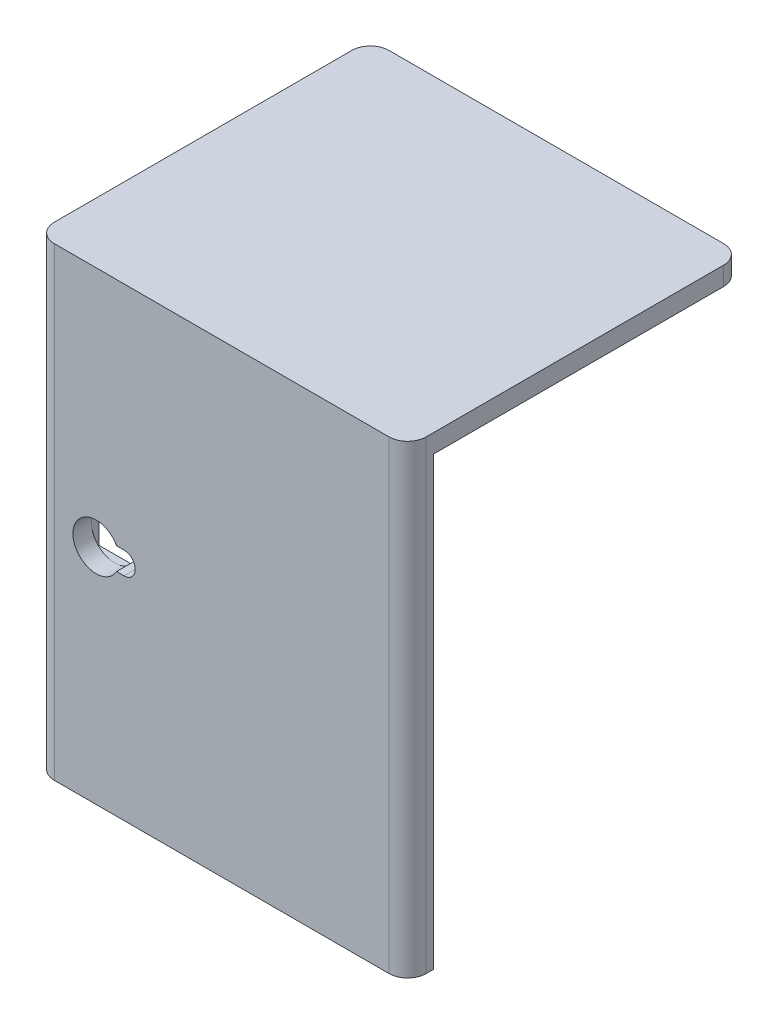
SolidWorks part; units mm, degrees
ref_plane "정면" through (0, 0, 0) normal (0, 0, 1) x (1, 0, 0)
ref_plane "윗면" through (0, 0, 0) normal (0, 1, 0) x (1, 0, 0)
ref_plane "우측면" through (0, 0, 0) normal (1, 0, 0) x (0, 0, -1)
sketch "스케치1" plane through (0, 0, 0) normal (0, 1, 0) x (1, 0, 0)
  line L1 (-50, -45) -> (50, -45)
  line L2 (-50, -45) -> (-50, 45)
  line L3 (-50, 45) -> (50, 45)
  line L4 (50, -45) -> (50, 45)
  line L5 (-50, -45) -> (50, 45) construction
  line L6 (-50, 45) -> (50, -45) construction
  point P0 (0, 0)
  dimension "D1" = 100
  dimension "D2" = 90
extrude "보스-돌출1" add sketch "스케치1" along normal blind 125
sketch "스케치4" plane through (0, 0, 0) normal (0, -1, 0) x (1, 0, 0)
  line L0 (50, 45) -> (50, 38) construction
  line L1 (50, 45) -> (50, -45) construction
  line L3 (-50, -45) -> (50, -45)
  line L4 (-50, -45) -> (-50, 38)
  line L5 (-50, 38) -> (50, 38)
  line L6 (50, -45) -> (50, 38)
  dimension "D1" = 7
extrude "컷-돌출3" cut sketch "스케치4" against normal blind 120
fillet "필렛4" radius 5 4 edges at (-50, 62.5, 45) (50, 62.5, 45) (50, 122.5, -45) (-50, 122.5, -45)
sketch "스케치5" plane through (0, 0, 38) normal (0, 0, -1) x (-1, 0, 0)
  line L0 (50, 125) -> (50, 60) construction
  line L1 (50, 120) -> (50, 0) construction
  line L2 (50, 60) -> (40, 60) construction
  line L4 (26.25, 63) -> (28.2671, 63)
  line L5 (26.25, 57) -> (28.2671, 57)
  arc A0 (28.2671, 57) -> (28.2671, 63) centre (33.75, 60) ccw
  arc A1 (26.25, 63) -> (26.25, 57) centre (26.25, 60) ccw
  dimension "D1" = 10
extrude "컷-돌출4" cut sketch "스케치5" against normal blind 120
sketch "스케치6" plane through (0, 0, 38) normal (0, 0, -1) x (-1, 0, 0)
  line L0 (40, 60) -> (40, 66.25) construction
  line L1 (40, 60) -> (40, 53.75) construction
  line L2 (40, 53.75) -> (17, 53.75) construction
  line L4 (40, 66.25) -> (17, 66.25)
  line L5 (40, 66.25) -> (40, 53.75)
  line L6 (40, 53.75) -> (17, 53.75)
  line L7 (17, 66.25) -> (17, 53.75)
  arc A0 (28.2671, 57) -> (28.2671, 63) centre (33.75, 60) ccw construction
  dimension "D1" = 23
  dimension "D2" = 12.5
extrude "컷-돌출5" cut sketch "스케치6" against normal blind 2
